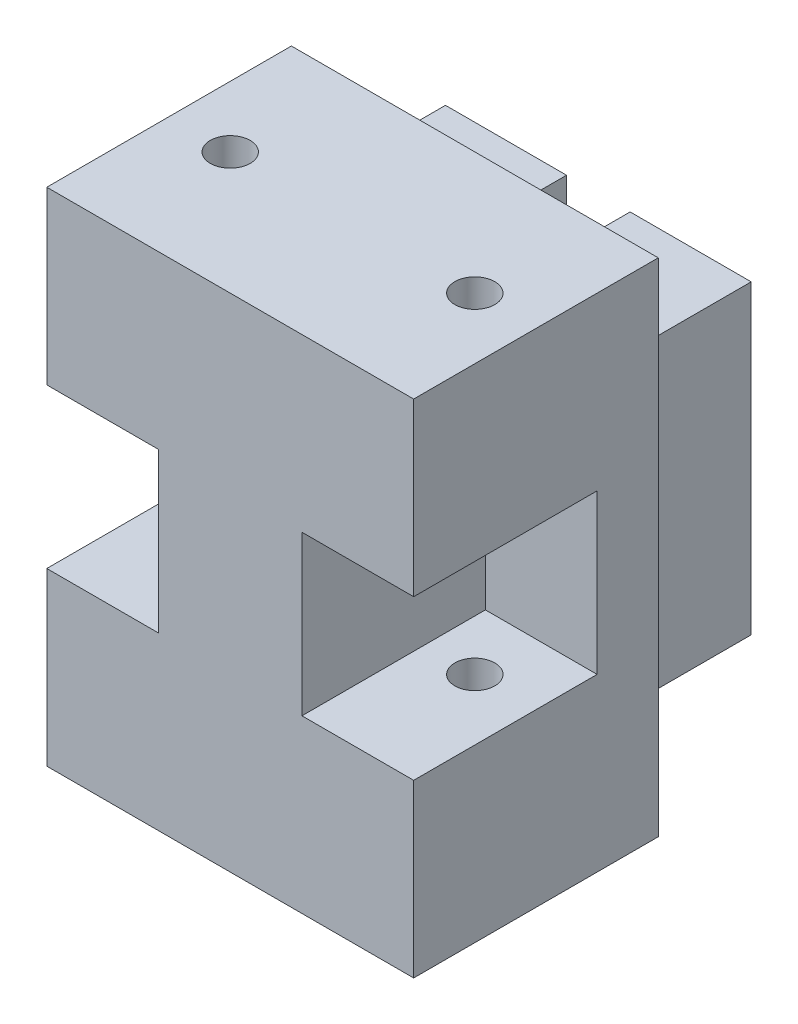
SolidWorks part; units mm, degrees
ref_plane "Front Plane" through (0, 0, 0) normal (0, 0, 1) x (1, 0, 0)
ref_plane "Top Plane" through (0, 0, 0) normal (0, 1, 0) x (1, 0, 0)
ref_plane "Right Plane" through (0, 0, 0) normal (1, 0, 0) x (0, 0, -1)
sketch "Sketch2" plane through (0, 0, 0) normal (0, 0, 1) x (1, 0, 0)
  line L0 (-15, 20.5) -> (-15, 6.5)
  line L1 (-15, 20.5) -> (15, 20.5)
  line L2 (-15, 20.5) -> (-15, -20.5)
  line L3 (-15, -20.5) -> (15, -20.5)
  line L4 (15, 20.5) -> (15, -20.5)
  line L5 (-15, 20.5) -> (15, -20.5) construction
  line L6 (-15, -20.5) -> (15, 20.5) construction
  line L7 (-15, 6.5) -> (-5.8649, 6.5)
  line L8 (-5.8649, 6.5) -> (-5.8649, -6.5)
  line L9 (-5.8649, -6.5) -> (-15, -6.5)
  line L10 (-15, -6.5) -> (-15, -20.5)
  line L11 (-15, -20.5) -> (0, -20.5)
  line L12 (-15, 20.5) -> (0, 20.5)
  line L13 (0, -34.2738) -> (0, 34.2738) construction
  line L14 (15, 20.5) -> (15, -20.5)
  line L15 (5.8649, -6.5) -> (15, -6.5)
  line L16 (5.8649, 6.5) -> (5.8649, -6.5)
  line L17 (15, 6.5) -> (5.8649, 6.5)
  line L18 (15, 20.5) -> (15, 6.5)
  point P0 (0, 0)
  point P15 (0, 0)
  point P19 (-10.4324, -6.5)
  dimension "D1" = 41
  dimension "D2" = 30
  dimension "D3" = 13
  dimension "D4" = 14
extrude "Boss-Extrude1" add sketch "Sketch2" along normal blind 20 contours L17 L4 L1 L0 L7 L8 L9 L2 L3 L14 L15 L16
sketch "Sketch3" plane through (0, 0, 0) normal (0, 1, 0) x (1, 0, 0)
  line L0 (0, 22.1827) -> (0, -22.1827) construction
  line L2 (-50.789, -10) -> (18.3991, -10) construction
  line L4 (-15, -20) -> (15, -20) construction
  circle A0 centre (-10, -10) radius 1.6321
  circle A1 centre (10, -10) radius 1.6321
  point P4 (0, 0)
  point P8 (-16.195, -10)
  dimension "D1" = 10
  dimension "D2" = 20
extrude "Cut-Extrude1" cut sketch "Sketch3" against normal through all both and the other way through all
sketch "Sketch4" plane through (0, 0, 0) normal (0, 0, 1) x (1, 0, 0)
  line L1 (-15, 20.5) -> (15, 20.5)
  line L2 (-15, 20.5) -> (-15, -20.5)
  line L3 (-15, -20.5) -> (15, -20.5)
  line L4 (15, 20.5) -> (15, -20.5)
extrude "Boss-Extrude2" add sketch "Sketch4" along normal blind 5
sketch "Sketch6" plane through (0, 0, 0) normal (0, 0, 1) x (1, 0, 0)
  line L1 (12.5, 12.5) -> (-12.5, 12.5)
  line L2 (12.5, 12.5) -> (12.5, -12.5)
  line L3 (12.5, -12.5) -> (-12.5, -12.5)
  line L4 (-12.5, 12.5) -> (-12.5, -12.5)
  line L5 (12.5, 12.5) -> (-12.5, -12.5) construction
  line L6 (12.5, -12.5) -> (-12.5, 12.5) construction
  point P0 (0, 0)
  dimension "D1" = 25
  dimension "D2" = 25
extrude "Boss-Extrude3" add sketch "Sketch6" against normal blind 20
sketch "Sketch7" plane through (0, 0, 0) normal (0, 1, 0) x (1, 0, 0)
  line L0 (-12.5, 5.15) -> (-2.6, 5.15)
  line L1 (-12.5, 20) -> (-12.5, 0) construction
  line L2 (-2.6, 5.15) -> (-2.6, 10.1)
  line L3 (0, -20.6817) -> (0, 20.6817) construction
  line L4 (-2.6, 10.1) -> (2.6, 10.1)
  line L5 (-12.5, 5.15) -> (-12.5, 0)
  line L6 (-12.5, 0) -> (0, 0)
  line L7 (-7.55, 5.15) -> (-7.55, 0)
  line L8 (7.55, 5.15) -> (7.55, 0)
  line L9 (12.5, 5.15) -> (2.6, 5.15)
  line L10 (2.6, 5.15) -> (2.6, 10.1)
  line L11 (-12.5, 0) -> (12.5, 0)
  line L12 (-15, 0) -> (15, 0) construction
  line L13 (12.5, 0) -> (-12.5, 0) construction
  point P9 (0, 0)
  point P21 (0, 10.1)
  dimension "D1" = 4.95
  dimension "D2" = 2.6
  dimension "D3" = 5.15
  dimension "D4" = 4.95
extrude "Cut-Extrude4" cut sketch "Sketch7" against normal blind 20 from offset 12.5 contours L6 L3 L4 L2 L0 L7 | L3 L11 L8 L9 L10 L4
sketch "Sketch8" plane through (0, 0, 0) normal (0, 1, 0) x (1, 0, 0)
  line L1 (-2.6, 10.1) -> (12.5, 10.1)
  line L2 (-2.6, 10.1) -> (-2.6, 20)
  line L3 (-2.6, 20) -> (12.5, 20)
  line L4 (12.5, 10.1) -> (12.5, 20)
  line L5 (-2.6, 10.1) -> (-12.5, 10.1)
  line L6 (-2.6, 10.1) -> (-2.6, 20)
  line L7 (-2.6, 20) -> (-12.5, 20)
  line L8 (-12.5, 10.1) -> (-12.5, 20)
extrude "Cut-Extrude5" cut sketch "Sketch8" against normal through all both and the other way through all contours L8 L5 L2 L7 | L1 L4 L3 L2
